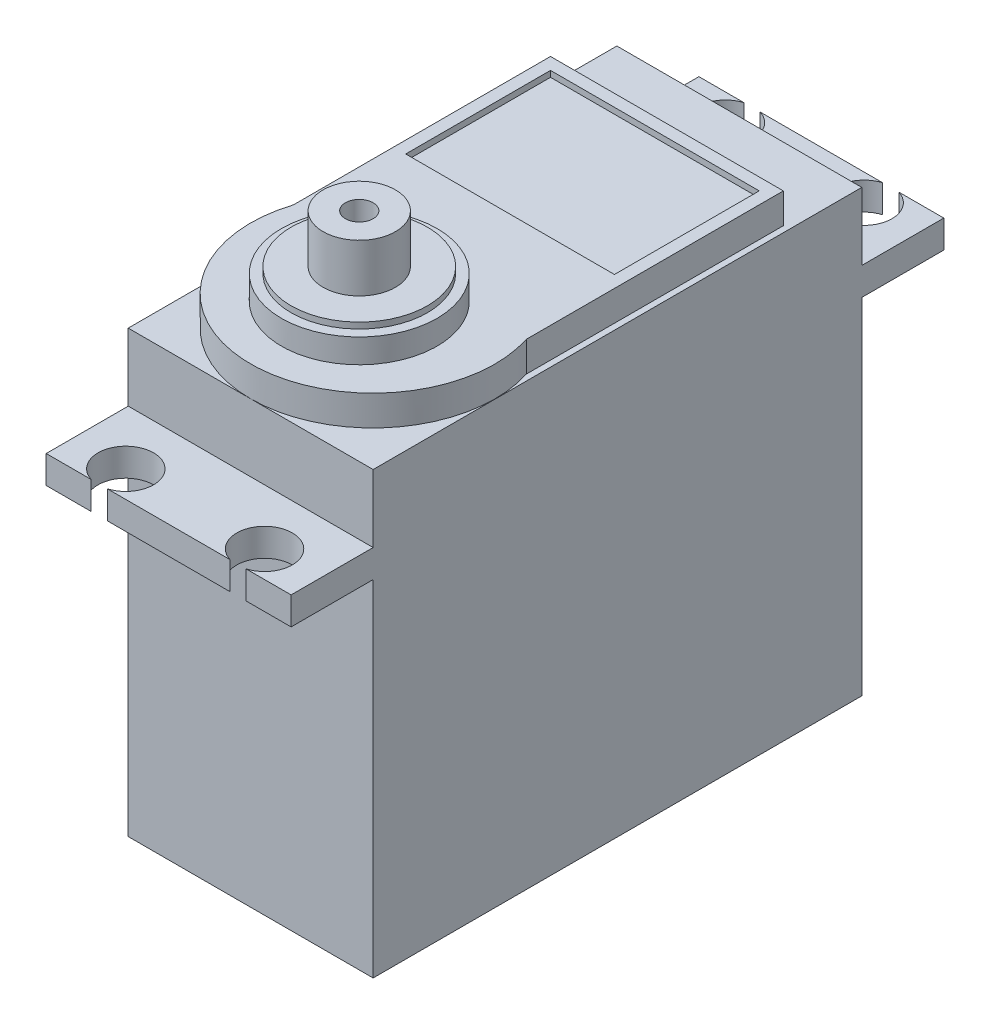
SolidWorks part; units mm, degrees
ref_plane "Front Plane" through (0, 0, 0) normal (0, 0, 1) x (1, 0, 0)
ref_plane "Top Plane" through (0, 0, 0) normal (0, 1, 0) x (1, 0, 0)
ref_plane "Right Plane" through (0, 0, 0) normal (1, 0, 0) x (0, 0, -1)
sketch "Sketch1" plane through (0, 0, 0) normal (0, 1, 0) x (1, 0, 0)
  line L1 (-10.15, -20.25) -> (10.15, -20.25)
  line L2 (-10.15, -20.25) -> (-10.15, 20.25)
  line L3 (-10.15, 20.25) -> (10.15, 20.25)
  line L4 (10.15, -20.25) -> (10.15, 20.25)
  line L5 (-10.15, -20.25) -> (10.15, 20.25) construction
  line L6 (-10.15, 20.25) -> (10.15, -20.25) construction
  point P0 (0, 0)
  dimension "D1" = 40.5
  dimension "D2" = 20.3
extrude "Boss-Extrude1" add sketch "Sketch1" along normal blind 36.5
sketch "Sketch4" plane through (0, 0, 20.25) normal (0, 0, 1) x (1, 0, 0)
  line L0 (10.15, 0) -> (10.15, 28.6) construction
  line L1 (10.15, 36.5) -> (10.15, 0) construction
  line L2 (10.15, 28.6) -> (-10.15, 28.6)
  line L3 (-10.15, 36.5) -> (-10.15, 0) construction
  line L4 (-10.15, 28.6) -> (-10.15, 30.9)
  line L5 (-10.15, 30.9) -> (10.15, 30.9)
  line L6 (10.15, 30.9) -> (10.15, 28.6)
  dimension "D1" = 28.6
  dimension "D2" = 2.3
extrude "Boss-Extrude4" add sketch "Sketch4" along normal blind 6.8 contours L5 L6 L2 L4
sketch "Sketch5" plane through (0, 30.9, 0) normal (0, 1, 0) x (1, 0, 0)
  line L0 (0, -20.25) -> (0, -22.35) construction
  line L1 (-10.15, -20.25) -> (10.15, -20.25) construction
  line L2 (-10.15, -22.35) -> (10.15, -22.35) construction
  line L3 (10.15, -27.05) -> (10.15, -20.25) construction
  line L4 (0, -22.35) -> (0, -27.05) construction
  line L5 (-10.15, -27.05) -> (10.15, -27.05) construction
  line L7 (10.15, -27.05) -> (8.05, -27.05) construction
  line L8 (8.05, -27.05) -> (5.75, -27.05)
  line L9 (5.75, -27.05) -> (5.75, -24.85)
  circle A0 centre (5.75, -24.85) radius 2.3
  circle A1 centre (-5.75, -24.85) radius 2.3
  point P10 (0, -22.35)
  dimension "D2" = 4.6
  dimension "D1" = 2.1
  dimension "D3" = 2.1
  dimension "D4" = 2.2
  dimension "D5" = 2.3
extrude "Cut-Extrude1" cut sketch "Sketch5" against normal up to body (2.3 mm away) separate body
sketch "Sketch6" plane through (-10.15, 0, 0) normal (-1, 0, 0) x (0, 0, 1)
  line L0 (0, 0) -> (0, 36.5) construction
  line L1 (-20.25, 0) -> (20.25, 0) construction
  line L2 (-20.25, 36.5) -> (20.25, 36.5) construction
ref_plane "Plane1" through (0, 0, 0) normal (0, 0, 1) x (0, 1, 0)
mirror "Mirror2" about plane through (0, 0, 0) normal (0, 0, 1) of "Cut-Extrude1", "Boss-Extrude4"
sketch "Sketch7" plane through (0, 36.5, 0) normal (0, 1, 0) x (1, 0, 0)
  line L0 (10.15, 20.25) -> (-10.15, 20.25) construction
  line L1 (10.15, -20.25) -> (10.15, 20.25) construction
  line L2 (10.15, 14.75) -> (-10.15, 14.75)
  line L3 (-10.15, 20.25) -> (-10.15, -20.25) construction
  line L4 (-10.15, 14.75) -> (-10.15, -7.05)
  line L5 (10.15, 14.75) -> (10.15, -7.05) construction
  line L6 (0, -20.25) -> (0, 11.25) construction
  line L7 (-10.15, -20.25) -> (10.15, -20.25) construction
  line L8 (-9.65, 14.25) -> (-9.65, -7.05)
  line L9 (9.65, 14.25) -> (-9.65, 14.25)
  line L10 (9.65, 14.25) -> (9.65, -7.05)
  arc A0 (9.65, -7.05) -> (-9.65, -7.05) centre (0, -10.1226) cw
  dimension "D1" = 5.5
  dimension "D2" = 13.2
  dimension "D3" = 31.5
  dimension "D4" = 0.5
extrude "Boss-Extrude5" add sketch "Sketch7" along normal blind 2.5 contours A0 L8 L9 L10
sketch "Sketch10" plane through (0, 39, 0) normal (0, 1, 0) x (1, 0, 0)
  line L0 (0, -20.25) -> (0, -11.25) construction
  arc A0 (-9.65, -7.05) -> (9.65, -7.05) centre (0, -10.1226) ccw construction
  circle A1 centre (0, -11.25) radius 6.45
  dimension "D2" = 12.9
  dimension "D1" = 9
extrude "Boss-Extrude6" add sketch "Sketch10" along normal blind 2
sketch "Sketch11" plane through (0, 41, 0) normal (0, 1, 0) x (1, 0, 0)
  circle A0 centre (0, -11.25) radius 6.45 construction
  circle A1 centre (0, -11.25) radius 5.65
  dimension "D1" = 0.8
extrude "Boss-Extrude7" add sketch "Sketch11" along normal blind 0.5
sketch "Sketch12" plane through (0, 41.5, 0) normal (0, 1, 0) x (1, 0, 0)
  circle A0 centre (0, -11.25) radius 3
  dimension "D1" = 6
extrude "Boss-Extrude8" add sketch "Sketch12" along normal blind 4
sketch "Sketch13" plane through (0, 45.5, 0) normal (0, 1, 0) x (1, 0, 0)
  circle A0 centre (0, -11.25) radius 1.15
  dimension "D1" = 2.3
extrude "Cut-Extrude2" cut sketch "Sketch13" against normal blind 4
sketch "Sketch14" plane through (0, 39, 0) normal (0, 1, 0) x (1, 0, 0)
  line L0 (9.65, 14.25) -> (-9.65, 14.25) construction
  line L1 (-8.65, 13.25) -> (8.65, 13.25)
  line L2 (-8.65, 13.25) -> (-8.65, 1.25)
  line L3 (-8.65, 1.25) -> (8.65, 1.25)
  line L4 (8.65, 13.25) -> (8.65, 1.25)
  line L5 (-9.65, 14.25) -> (-9.65, -7.05) construction
  line L6 (9.65, 14.25) -> (9.65, -7.05) construction
  dimension "D1" = 1
  dimension "D2" = 1
  dimension "D3" = 1
  dimension "D4" = 12
extrude "Cut-Extrude3" cut sketch "Sketch14" against normal blind 0.5
equation "\"SpoolCenterToMotor\" = 31.5mm"
equation "\"D3@Sketch7\"=\"SpoolCenterToMotor\""
equation "\"MotorLength\" = 40.5mm"
equation "\"D1@Sketch1\"=\"MotorLength\""
equation "\"MotorWidth\" = 20.3mm"
equation "\"D2@Sketch1\"=\"MotorWidth\""
equation "\"AttachmentHeight\"= 3mm"
equation "\"SpoolDiameter\"= 60mm"
equation "\"SpoolHeight\"= 2mm"
equation "\"SpoolRidgeHeight\"= 1mm"
equation "\"SpoolRidgeDepth\"= 2mm"
equation "\"OuterThickness\"= 3mm"
equation "\"MasterFillet\"= 3mm"
equation "\"PartSeperation\"= 6mm"
equation "\"Tolerance\"= 0.15mm"
equation "\"HeightPart\"= 100mm"
equation "\"Holes\"= 1.5mm"
equation "\"SpineHolderThickness\"= 3mm"
equation "\"SpineHolderDepth\" = 3mm"
equation "\"MotorTransmitterToScrew\"= 21.7mm"
equation "\"SpoolSeperation\"= 2mm"
equation "\"ServoHolderWidthOffset\"= 20mm"
equation "\"DiscThickness\"= 4mm"
equation "\"LigamentThickness\"= 2mm"
equation "\"LigamentExtension\"= 1mm"
equation "\"LigamentAngle\"= 20deg"
equation "\"SpineDiameter\"= 15mm"
equation "\"LigamentDepth\"= 1mm"
equation "\"SpoolToSpine\"= 15mm"
equation "\"HubOffset\"= 18mm"
equation "\"ServoFastenerHolders\"=2mm"
equation "\"ArduinoLength\" = 53.4mm"
equation "\"ArduinoWidth\" = 50mm"
equation "\"ArdYOffset\" = 29.5mm"
equation "\"ArdXOffset\" = 20.5mm"
equation "\"ArdXOffsetSmall\" = 25mm"
equation "\"MiddleServoOffset\"= 12mm"
equation "\"LargeServoOffset\"= 3mm"
equation "\"SmallServoOffset\"= 0mm"
equation "\"ToolHoleDiameter\"= 12mm"
